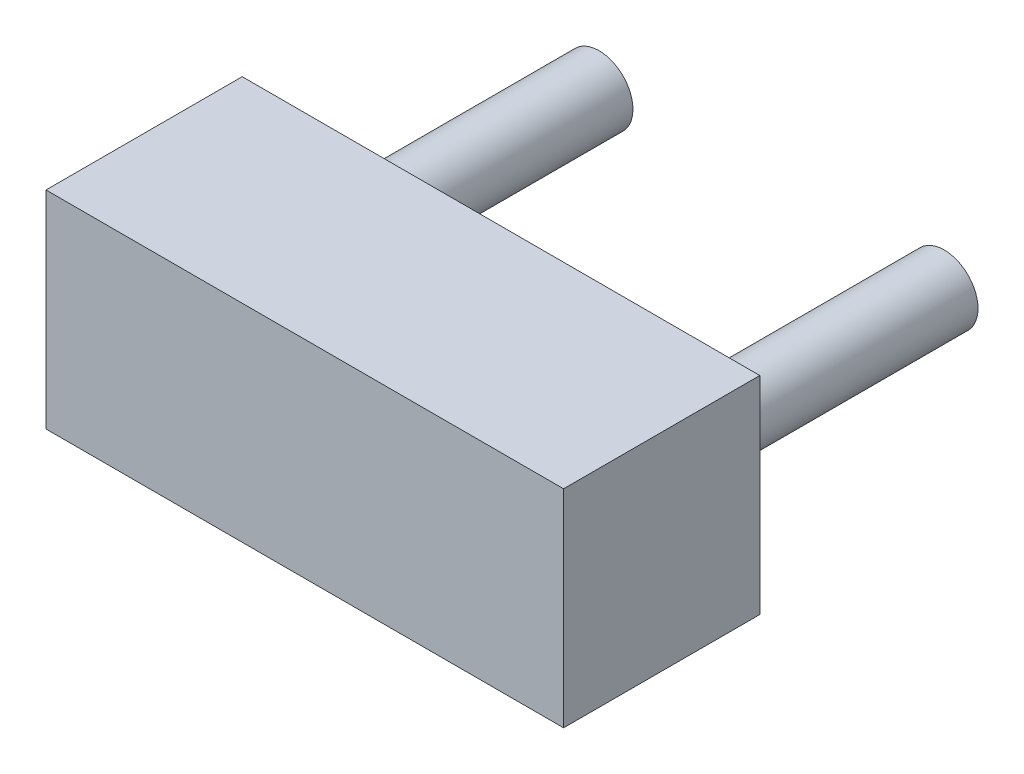
SolidWorks part; units mm, degrees
ref_plane "Front Plane" through (0, 0, 0) normal (0, 0, 1) x (1, 0, 0)
ref_plane "Top Plane" through (0, 0, 0) normal (0, 1, 0) x (1, 0, 0)
ref_plane "Right Plane" through (0, 0, 0) normal (1, 0, 0) x (0, 0, -1)
sketch "Sketch1" plane through (0, 0, 0) normal (0, 0, 1) x (1, 0, 0)
  line L0 (-1.9125, 0.765) -> (-1.9125, -0.765)
  line L1 (-1.9125, -0.765) -> (1.9125, -0.765)
  line L2 (1.9125, -0.765) -> (1.9125, 0.765)
  line L3 (1.9125, 0.765) -> (-1.9125, 0.765)
extrude "Component_Outline" add sketch "Sketch1" along normal blind 1.45 separate body
sketch "Sketch2" plane through (0, 0, 0) normal (0, 0, 1) x (1, 0, 0)
  circle A0 centre (-1.275, 0) radius 0.25
extrude "1" add sketch "Sketch2" against normal blind 2 separate body
sketch "Sketch3" plane through (0, 0, 0) normal (0, 0, 1) x (1, 0, 0)
  circle A0 centre (1.275, 0) radius 0.25
extrude "2" add sketch "Sketch3" against normal blind 2 separate body
sketch3d "3DSketch1"
  line L0 (0, 0, 0) -> (1, 0, 0)
  line L1 (0, 0, 0) -> (0, 1, 0)
  line L2 (0, 0, 0) -> (0, 0, 1)
  point P0 (0, 0, 0)
